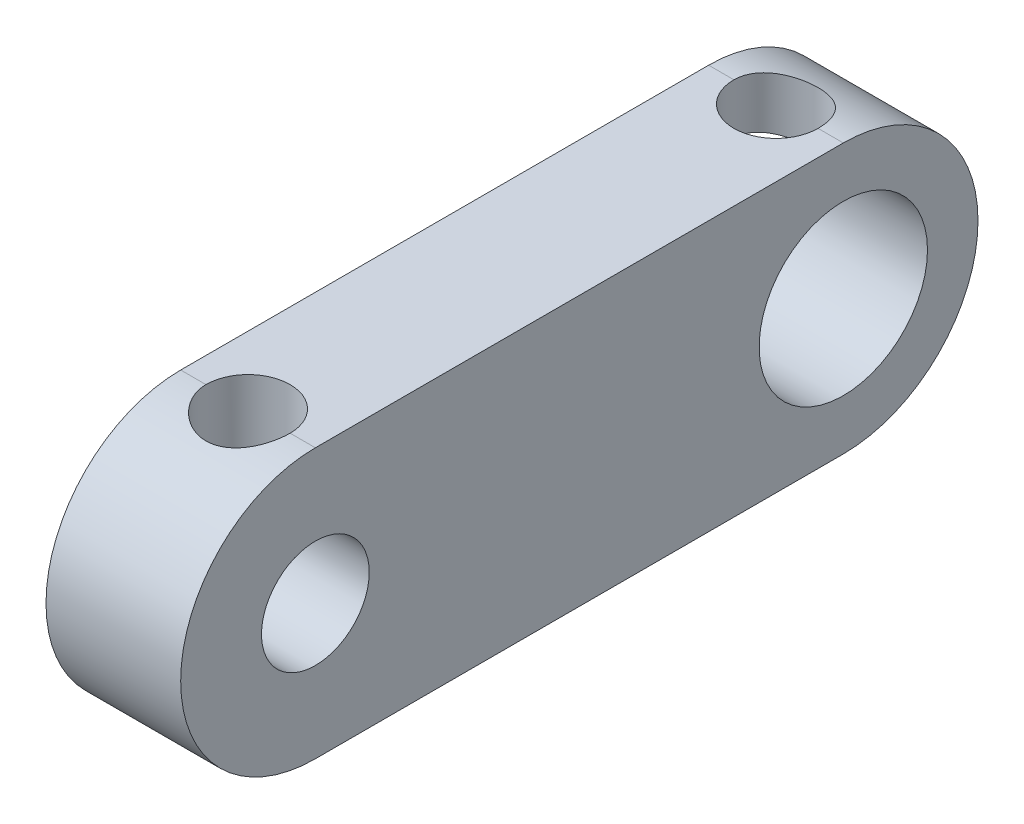
SolidWorks part; units mm, degrees
material "1060 Alloy"
ref_plane "Front Plane" through (0, 0, 0) normal (0, 0, 1) x (1, 0, 0)
ref_plane "Top Plane" through (0, 0, 0) normal (0, 1, 0) x (1, 0, 0)
ref_plane "Right Plane" through (0, 0, 0) normal (1, 0, 0) x (0, 0, -1)
sketch "Sketch1" plane through (0, 0, 0) normal (1, 0, 0) x (0, 0, -1)
  line L0 (0, 0) -> (15.68, 0) construction
  line L1 (0, 4) -> (15.68, 4)
  line L2 (0, -4) -> (15.68, -4)
  arc A0 (0, 4) -> (0, -4) centre (0, 0) ccw
  arc A1 (15.68, -4) -> (15.68, 4) centre (15.68, 0) ccw
  circle A2 centre (0, 0) radius 1.6
  circle A3 centre (15.68, 0) radius 2.5
  point P3 (7.84, 0)
  dimension "D1" = 4
  dimension "D2" = 3.2
  dimension "D4" = 5
  dimension "D3" = 15.68
extrude "Boss-Extrude1" add sketch "Sketch1" along normal mid plane 4
hole_wizard "M3x0.5 Tapped Hole1" positions "Sketch2" profile "Sketch3" tap size "M3x0.5" standard "ANSI Metric"
sketch "Sketch2" plane through (0, 4, 0) normal (0, 1, 0) x (1, 0, 0)
  line L0 (2, 15.68) -> (-2, 15.68) construction
  point P0 (0, 15.68)
  point P4 (0, 0)
cosmetic thread "Hole Thread1"
cosmetic thread "Hole Thread2"
sketch "Sketch3" plane through (0, 4, -15.68) normal (1, 0, 0) x (0, 0, 1)
  line L0 (0, 0) -> (0, 5.7511)
  line L1 (0, 5.7511) -> (1.25, 5)
  line L2 (1.25, 5) -> (1.25, 0)
  line L5 (1.25, 0) -> (0, 0)
  line L10 (0, 5.7511) -> (-1.25, 5) construction
  line L11 (0, -6.35) -> (0, 107.95) construction
  dimension "Tap Drill Dia." = 2.5
  dimension "Tap Drill Depth" = 5
  dimension "Drill Angle" = 118
